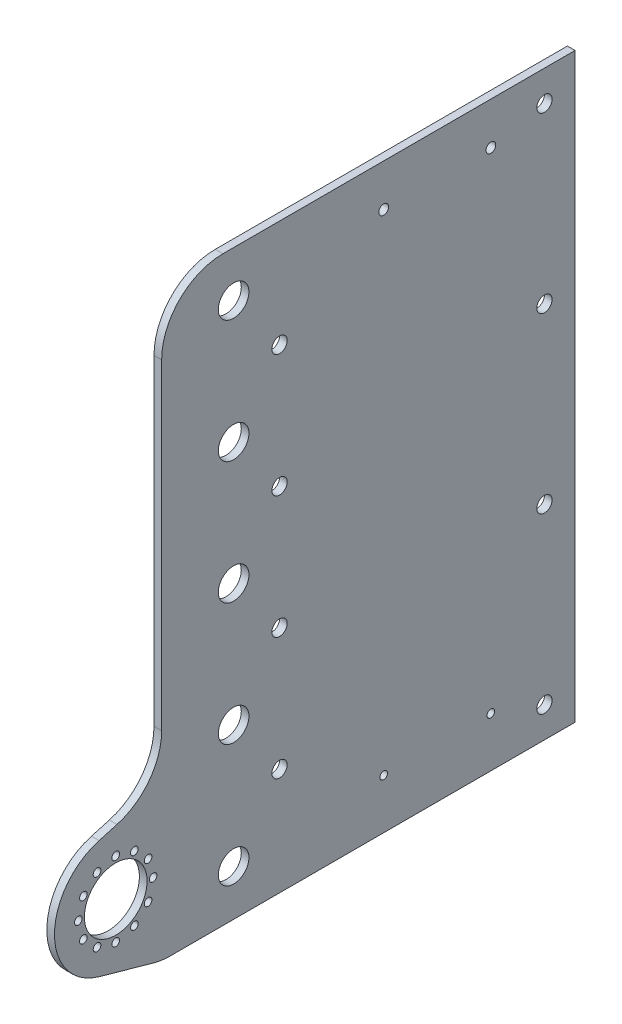
SolidWorks part; units mm, degrees
material "6061-T6 (SS)"
ref_plane "Front Plane" through (0, 0, 0) normal (0, 0, 1) x (1, 0, 0)
ref_plane "Top Plane" through (0, 0, 0) normal (0, 1, 0) x (1, 0, 0)
ref_plane "Right Plane" through (0, 0, 0) normal (1, 0, 0) x (0, 0, -1)
sketch "Sketch1" plane through (0, 0, 0) normal (1, 0, 0) x (0, 0, -1)
  line L0 (-85.725, -120.65) -> (-111.6578, -113.3497)
  line L1 (-85.725, 120.65) -> (85.725, 120.65)
  line L2 (-85.725, 120.65) -> (-85.725, -120.65) construction
  line L3 (-85.725, -120.65) -> (85.725, -120.65)
  line L4 (85.725, 120.65) -> (85.725, -120.65)
  line L5 (-85.725, 120.65) -> (85.725, -120.65) construction
  line L6 (-85.725, -120.65) -> (85.725, 120.65) construction
  line L7 (-111.6578, -64.4503) -> (-85.725, -57.15)
  line L8 (-85.725, 120.65) -> (-85.725, -57.15)
  arc A0 (-111.6578, -113.3497) -> (-111.6578, -64.4503) centre (-104.775, -88.9) cw
  point P0 (0, 0)
  dimension "D3" = 25.4
  dimension "D1" = 241.3
  dimension "D2" = 171.45
  dimension "D4" = 19.05
  dimension "D5" = 63.5
extrude "Boss-Extrude1" add sketch "Sketch1" along normal blind 3.175
sketch "Sketch2" plane through (3.175, 0, 0) normal (1, 0, 0) x (0, 0, -1)
  line L0 (-55.88, -101.6) -> (-55.88, -50.8) construction
  line L1 (-55.88, -50.8) -> (-36.83, -76.2) construction
  line L2 (-36.83, -76.2) -> (-55.88, -101.6) construction
  line L3 (-36.83, -76.2) -> (-36.83, -25.4) construction
  line L4 (-40.0376, -100.5834) -> (-41.5827, -76.505) construction
  circle A0 centre (73.025, -107.95) radius 3.175 construction
  circle A1 centre (73.025, -35.9833) radius 3.175 construction
  circle A2 centre (73.025, 35.9833) radius 3.175 construction
  circle A3 centre (73.025, 107.95) radius 3.175 construction
  circle A4 centre (-55.88, -101.6) radius 6.35 construction
  circle A5 centre (-55.88, -50.8) radius 6.35 construction
  circle A6 centre (-55.88, 0) radius 6.35 construction
  circle A7 centre (-55.88, 50.8) radius 6.35 construction
  circle A8 centre (-55.88, 101.6) radius 6.35 construction
  circle A9 centre (73.025, -107.95) radius 3.175
  circle A10 centre (73.025, -35.9833) radius 3.175
  circle A11 centre (73.025, 35.9833) radius 3.175
  circle A12 centre (73.025, 107.95) radius 3.175
  circle A13 centre (-55.88, -101.6) radius 6.35
  circle A14 centre (-55.88, -50.8) radius 6.35
  circle A15 centre (-55.88, 0) radius 6.35
  circle A16 centre (-55.88, 50.8) radius 6.35
  circle A17 centre (-55.88, 101.6) radius 6.35
  circle A18 centre (-36.83, -76.2) radius 3.175
  circle A19 centre (-36.83, -25.4) radius 3.175
  circle A20 centre (-36.83, 25.4) radius 3.175
  circle A21 centre (-36.83, 76.2) radius 3.175
  circle A22 centre (-97.775, -88.9) radius 6 construction
  circle A23 centre (-97.775, -88.9) radius 6 construction
  circle A24 centre (-36.83, -76.2) radius 4.7625 construction
  circle A25 centre (-55.88, -101.6) radius 15.875 construction
  circle A26 centre (-91.3516, -96.65) radius 1.25 construction
  circle A27 centre (-104.775, -104.4) radius 1.25 construction
  circle A28 centre (-118.1984, -96.65) radius 1.25 construction
  circle A29 centre (-118.1984, -81.15) radius 1.25 construction
  circle A30 centre (-104.775, -73.4) radius 1.25 construction
  circle A31 centre (-91.3516, -81.15) radius 1.25 construction
  circle A32 centre (-91.3516, -96.65) radius 1.25 construction
  circle A33 centre (-104.775, -104.4) radius 1.25 construction
  circle A34 centre (-118.1984, -96.65) radius 1.25 construction
  circle A35 centre (-118.1984, -81.15) radius 1.25 construction
  circle A36 centre (-104.775, -73.4) radius 1.25 construction
  circle A37 centre (-91.3516, -81.15) radius 1.25 construction
  circle A38 centre (-104.775, -88.9) radius 15.5 construction
  circle A39 centre (-104.775, -88.9) radius 13
  circle A40 centre (-104.775, -73.4) radius 1.5875
  circle A41 centre (-97.025, -75.4766) radius 1.5875
  circle A42 centre (-91.3516, -81.15) radius 1.5875
  circle A43 centre (-89.275, -88.9) radius 1.5875
  circle A44 centre (-91.3516, -96.65) radius 1.5875
  circle A45 centre (-97.025, -102.3234) radius 1.5875
  circle A46 centre (-104.775, -104.4) radius 1.5875
  circle A47 centre (-112.525, -102.3234) radius 1.5875
  circle A48 centre (-118.1984, -96.65) radius 1.5875
  circle A49 centre (-120.275, -88.9) radius 1.5875
  circle A50 centre (-118.1984, -81.15) radius 1.5875
  circle A51 centre (-112.525, -75.4766) radius 1.5875
  circle A52 centre (6.35, 103.1875) radius 2.032 construction
  circle A53 centre (50.8, 103.1875) radius 2.032 construction
  circle A54 centre (6.35, 103.1875) radius 2.032
  circle A55 centre (50.8, 103.1875) radius 2.032
  circle A56 centre (50.8, -100.0125) radius 1.5875 construction
  circle A57 centre (6.35, -100.0125) radius 1.5875 construction
  circle A58 centre (50.8, -100.0125) radius 1.5875
  circle A59 centre (6.35, -100.0125) radius 1.5875
  point P100 (-104.775, -88.9)
  dimension "D1" = 6.35
  dimension "D3" = 9.525
  dimension "D4" = 31.75
  dimension "D6" = 3.175
  dimension "D5" = 19.05
  dimension "D2" = 4
  dimension "D7" = 12
extrude "Cut-Extrude1" cut sketch "Sketch2" against normal through all
fillet "Fillet1" radius 25.4 3 edges at (1.5875, -120.65, 85.725) (1.5875, 120.65, 85.725) (1.5875, -57.15, 85.725)
